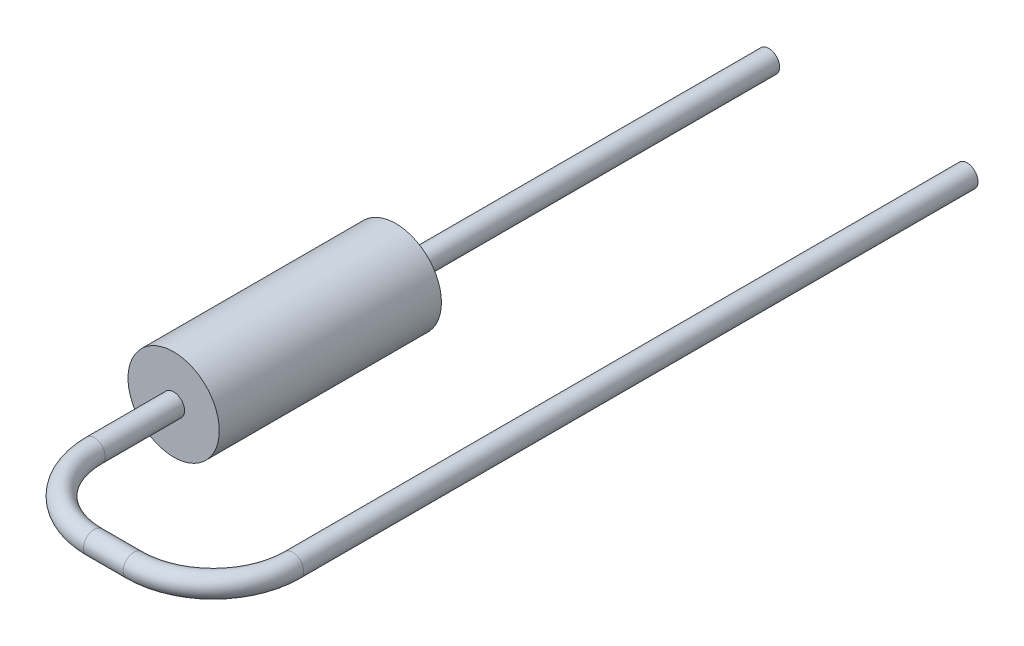
SolidWorks part; units mm, degrees
ref_plane "Front Plane" through (0, 0, 0) normal (0, 0, 1) x (1, 0, 0)
ref_plane "Top Plane" through (0, 0, 0) normal (0, 1, 0) x (1, 0, 0)
ref_plane "Right Plane" through (0, 0, 0) normal (1, 0, 0) x (0, 0, -1)
sketch "Sketch2" plane through (0, 0, 0) normal (0, 0, 1) x (1, 0, 0)
  circle A0 centre (0, 0) radius 1.15
  dimension "D1" = 2.3
extrude "Resistor Body" add sketch "Sketch2" along normal blind 5.6
sketch "Lead1 Path" plane through (0, 0, 0) normal (0, 1, 0) x (1, 0, 0)
  line L1 (-1.15, -5.6) -> (1.15, -5.6) construction
  line L2 (0, -5.6) -> (0, 0) construction
  line L3 (0, -5.6) -> (0, -7.6)
  line L4 (5, -7.6) -> (5, 9.4)
  line L5 (2, -9.6) -> (3, -9.6)
  arc A0 (0, -7.6) -> (2, -9.6) centre (2, -7.6) ccw
  arc A1 (5, -7.6) -> (3, -9.6) centre (3, -7.6) cw
  point P11 (0, -9.6)
  point P14 (5, -9.6)
  dimension "D4" = 2
  dimension "D1" = 4
  dimension "D2" = 19
  dimension "D3" = 5
sketch "Lead1 Profile" plane through (0, 0, 5.6) normal (0, 0, 1) x (-1, 0, 0)
  circle A0 centre (0, 0) radius 0.275
  dimension "D1" = 0.55
sweep "Lead1" add profiles "Lead1 Profile" path "Lead1 Path"
sketch "Sketch6" plane through (0, 0, 0) normal (0, 0, -1) x (1, 0, 0)
  circle A0 centre (0, 0) radius 0.275 construction
  circle A1 centre (0, 0) radius 0.275
extrude "Lead2" add sketch "Sketch6" along normal up to surface (9.4 mm away) up to face at (4.725, 0, -9.4)
ref_plane "Mouting Plane" through (0, 0, -5.5) normal (0, 0, 1) x (1, 0, 0)
sketch "Component_Outline" plane through (0, 0, -5.5) normal (0, 0, 1) x (1, 0, 0)
  line L0 (1.1166, 0.275) -> (5, 0.275)
  line L1 (2, 0.275) -> (0, 0.275) construction
  line L2 (5, -0.275) -> (1.1166, -0.275)
  line L3 (0, -0.275) -> (2, -0.275) construction
  arc A0 (1.1166, 0.275) -> (1.1166, -0.275) centre (0, 0) ccw
  circle A1 centre (5, 0) radius 0.275 construction
  arc A2 (5, 0.275) -> (5, -0.275) centre (5, 0) cw
  dimension "D1" = 1.15
